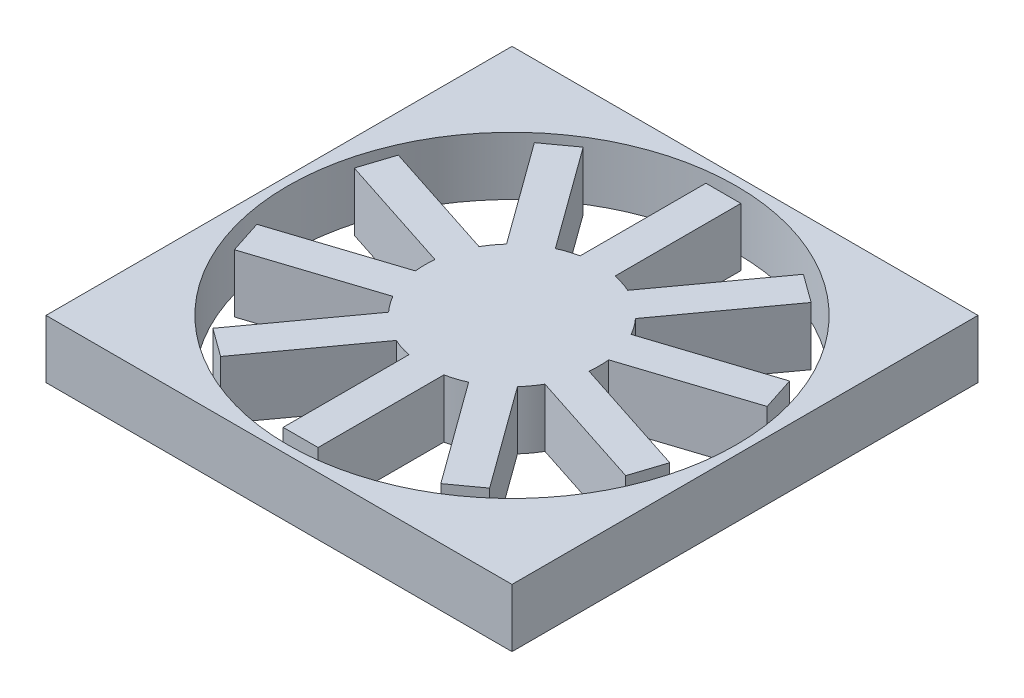
SolidWorks part; units mm, degrees
ref_plane "Front Plane" through (0, 0, 0) normal (0, 0, 1) x (1, 0, 0)
ref_plane "Top Plane" through (0, 0, 0) normal (0, 1, 0) x (1, 0, 0)
ref_plane "Right Plane" through (0, 0, 0) normal (1, 0, 0) x (0, 0, -1)
sketch "Sketch1" plane through (0, 0, 0) normal (0, 1, 0) x (1, 0, 0)
  line L1 (-28.6308, 39.5147) -> (51.3692, 39.5147)
  line L2 (-28.6308, 39.5147) -> (-28.6308, -40.4853)
  line L3 (-28.6308, -40.4853) -> (51.3692, -40.4853)
  line L4 (51.3692, 39.5147) -> (51.3692, -40.4853)
  dimension "D1" = 80
  dimension "D2" = 80
extrude "Boss-Extrude1" add sketch "Sketch1" along normal blind 10
sketch "Sketch2" plane through (0, 10, 0) normal (0, 1, 0) x (1, 0, 0)
  line L0 (51.3692, -40.4853) -> (51.3692, 39.5147) construction
  line L1 (-28.6308, -40.4853) -> (51.3692, -40.4853) construction
  circle A0 centre (11.3692, -0.4853) radius 38.5
  circle A1 centre (11.3692, -0.4853) radius 15
  dimension "D1" = 77
  dimension "D2" = 40
  dimension "D3" = 40
  dimension "D4" = 30
extrude "Cut-Extrude1" cut sketch "Sketch2" against normal blind 10
sketch "Sketch3" plane through (0, 10, 0) normal (0, 1, 0) x (1, 0, 0)
  line L0 (-12.3885, 27.1104) -> (3.4471, 5.3146)
  line L1 (8.3692, 35.8045) -> (14.3692, 35.8045)
  line L2 (8.3692, 35.8045) -> (8.3692, 8.8634)
  line L3 (8.3692, 8.8634) -> (14.3692, 8.8634)
  line L4 (14.3692, 35.8045) -> (14.3692, 8.8634)
  line L5 (-12.3885, 27.1104) -> (-7.5344, 30.6371)
  line L6 (-7.5344, 30.6371) -> (8.3012, 8.8413)
  line L7 (3.4471, 5.3146) -> (8.3012, 8.8413)
  line L8 (-24.0715, 7.8757) -> (1.551, -0.4495)
  line L9 (-24.0715, 7.8757) -> (-22.2174, 13.582)
  line L10 (-22.2174, 13.582) -> (3.4051, 5.2568)
  line L11 (1.551, -0.4495) -> (3.4051, 5.2568)
  line L12 (-22.2174, -14.5526) -> (3.4051, -6.2273)
  line L13 (-22.2174, -14.5526) -> (-24.0715, -8.8462)
  line L14 (-24.0715, -8.8462) -> (1.551, -0.521)
  line L15 (3.4051, -6.2273) -> (1.551, -0.521)
  line L16 (-7.5344, -31.6076) -> (8.3012, -9.8118)
  line L17 (-7.5344, -31.6076) -> (-12.3885, -28.0809)
  line L18 (-12.3885, -28.0809) -> (3.4471, -6.2851)
  line L19 (8.3012, -9.8118) -> (3.4471, -6.2851)
  line L20 (14.3692, -36.775) -> (14.3692, -9.8339)
  line L21 (14.3692, -36.775) -> (8.3692, -36.775)
  line L22 (8.3692, -36.775) -> (8.3692, -9.8339)
  line L23 (14.3692, -9.8339) -> (8.3692, -9.8339)
  line L24 (35.1268, -28.0809) -> (19.2912, -6.2851)
  line L25 (35.1268, -28.0809) -> (30.2727, -31.6076)
  line L26 (30.2727, -31.6076) -> (14.4371, -9.8118)
  line L27 (19.2912, -6.2851) -> (14.4371, -9.8118)
  line L28 (46.8098, -8.8462) -> (21.1873, -0.521)
  line L29 (46.8098, -8.8462) -> (44.9557, -14.5526)
  line L30 (44.9557, -14.5526) -> (19.3332, -6.2273)
  line L31 (21.1873, -0.521) -> (19.3332, -6.2273)
  line L32 (44.9557, 13.582) -> (19.3332, 5.2568)
  line L33 (44.9557, 13.582) -> (46.8098, 7.8757)
  line L34 (46.8098, 7.8757) -> (21.1873, -0.4495)
  line L35 (19.3332, 5.2568) -> (21.1873, -0.4495)
  line L36 (30.2727, 30.6371) -> (14.4371, 8.8413)
  line L37 (30.2727, 30.6371) -> (35.1268, 27.1104)
  line L38 (35.1268, 27.1104) -> (19.2912, 5.3146)
  line L39 (14.4371, 8.8413) -> (19.2912, 5.3146)
  circle A0 centre (11.3692, -0.4853) radius 15 construction
  point P44 (11.3692, -0.4853)
  dimension "D1" = 3
  dimension "D2" = 3
  dimension "D3" = 10
extrude "Boss-Extrude2" add sketch "Sketch3" against normal blind 10
